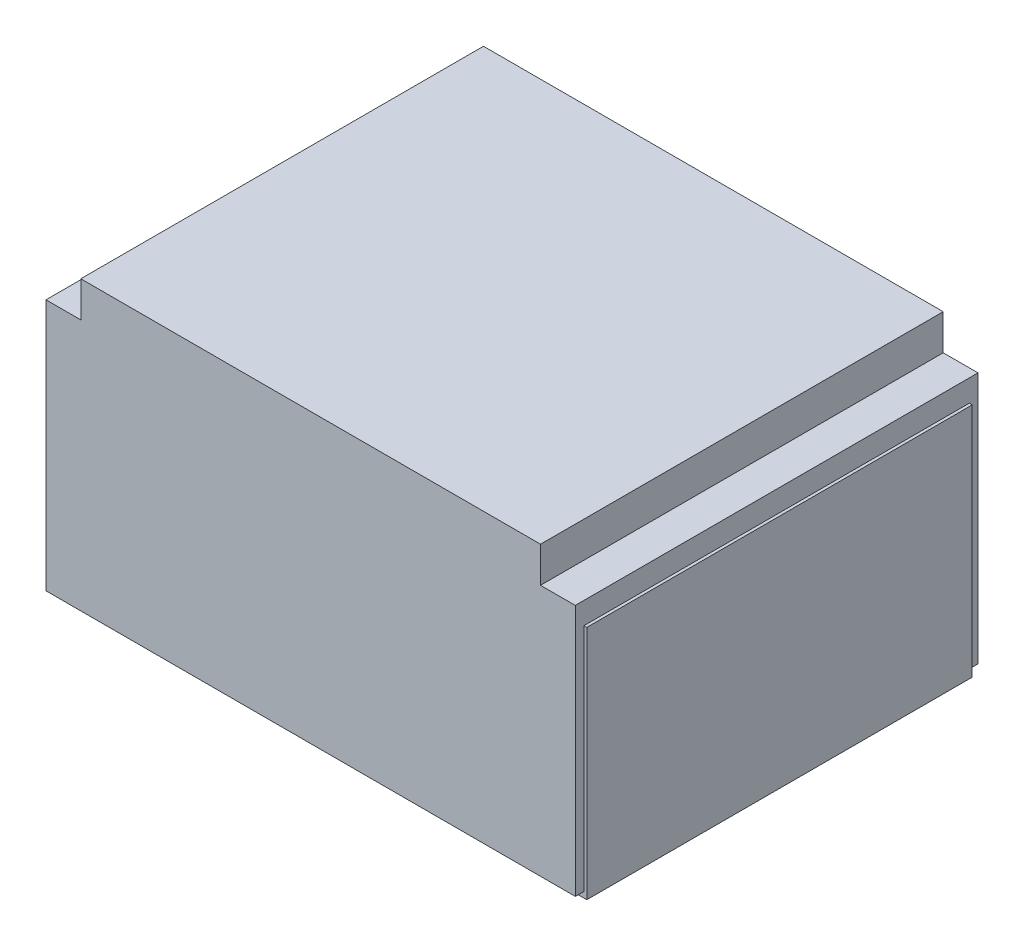
SolidWorks part; units mm, degrees
ref_plane "Płaszczyzna przednia" through (0, 0, 0) normal (0, 0, 1) x (1, 0, 0)
ref_plane "Płaszczyzna górna" through (0, 0, 0) normal (0, 1, 0) x (1, 0, 0)
ref_plane "Płaszczyzna prawa" through (0, 0, 0) normal (1, 0, 0) x (0, 0, -1)
sketch "Szkic1" plane through (0, 0, 0) normal (0, 0, 1) x (1, 0, 0)
  line L1 (2.3, 1.25) -> (-2.3, 1.25)
  line L2 (2.3, 1.25) -> (2.3, -1.25)
  line L3 (2.3, -1.25) -> (-2.3, -1.25)
  line L4 (-2.3, 1.25) -> (-2.3, -1.25)
  line L5 (2.3, 1.25) -> (-2.3, -1.25) construction
  line L6 (2.3, -1.25) -> (-2.3, 1.25) construction
  point P0 (0, 0)
  dimension "D1" = 2.5
  dimension "D2" = 4.6
extrude "Dodanie-wyciągnięcie1" add sketch "Szkic1" along normal blind 3.5
sketch "Szkic2" plane through (0, 0, 3.5) normal (0, 0, 1) x (1, 0, 0)
  line L0 (-2.3, 1.25) -> (-2.3, 0.9406)
  line L1 (-2.3, 1.25) -> (-2.3, -1.25) construction
  line L2 (-2.3, 0.9406) -> (-1.9978, 0.9406)
  line L3 (-1.9978, 0.9406) -> (-1.9978, 1.25)
  line L4 (2.3, 1.25) -> (-2.3, 1.25) construction
  line L5 (-1.9978, 1.25) -> (-2.3, 1.25)
  line L6 (0, 1.25) -> (0, 1.6855) construction
  line L7 (1.9978, 1.25) -> (2.3, 1.25)
  line L8 (1.9978, 0.9406) -> (1.9978, 1.25)
  line L9 (2.3, 0.9406) -> (1.9978, 0.9406)
  line L10 (2.3, 1.25) -> (2.3, 0.9406)
extrude "Wytnij-wyciągnięcie1" cut sketch "Szkic2" against normal through all
sketch "Szkic3" plane through (0, -1.25, 0) normal (0, -1, 0) x (1, 0, 0)
  line L0 (0, 3.5) -> (0, 0) construction
  line L1 (-2.3, 3.5) -> (2.3, 3.5) construction
  line L3 (-2.325, 0.075) -> (2.325, 0.075)
  line L4 (-2.325, 0.075) -> (-2.325, 3.425)
  line L5 (-2.325, 3.425) -> (2.325, 3.425)
  line L6 (2.325, 0.075) -> (2.325, 3.425)
  line L7 (-2.325, 0.075) -> (2.325, 3.425) construction
  line L8 (-2.325, 3.425) -> (2.325, 0.075) construction
  point P5 (0, 1.75)
  dimension "D1" = 3.35
  dimension "D2" = 4.65
extrude "Dodanie-wyciągnięcie2" add sketch "Szkic3" along normal blind 0.05 separate body
sketch "Szkic4" plane through (0, -1.3, 0) normal (0, -1, 0) x (1, 0, 0)
  line L0 (0, 3.425) -> (0, -0.2332) construction
  line L1 (2.325, 3.425) -> (-2.325, 3.425) construction
  line L2 (-1.7482, 0.075) -> (-1.7482, 0.4413)
  line L3 (-2.325, 0.075) -> (2.325, 0.075) construction
  line L4 (-1.7482, 0.4413) -> (-1.6483, 0.4413)
  line L5 (-1.6483, 0.4413) -> (-1.4734, 0.1915)
  line L6 (-1.4734, 0.1915) -> (1.4734, 0.1915)
  line L7 (1.6483, 0.4413) -> (1.4734, 0.1915)
  line L8 (1.7482, 0.4413) -> (1.6483, 0.4413)
  line L9 (1.7482, 0.075) -> (1.7482, 0.4413)
  line L10 (-1.7482, 0.075) -> (1.7482, 0.075)
  circle A0 centre (-1.9231, 3.0894) radius 0.1624
  circle A1 centre (1.9231, 3.0894) radius 0.1624
  circle A2 centre (0, 1.5959) radius 1.05
  point P17 (0, 0.1915)
  dimension "D1" = 2.1
extrude "Wytnij-wyciągnięcie2" cut sketch "Szkic4" against normal up to vertex (0.05 mm away)
sketch "Szkic5" plane through (0, -1.25, 0) normal (0, -1, 0) x (1, 0, 0)
  circle A0 centre (0, 1.5959) radius 1
  dimension "D1" = 2
extrude "Dodanie-wyciągnięcie3" add sketch "Szkic5" along normal blind 0.4 separate body
fillet "Zaokrąglenie1" radius 0.05 1 edges at (1, -1.65, 1.5959)
sketch "Szkic6" plane through (0, -1.25, 0) normal (0, 1, 0) x (1, 0, 0)
  line L0 (-2.325, -0.075) -> (-2.325, -3.425)
  line L1 (-2.325, -3.425) -> (-2.3, -3.425)
  line L2 (-2.3, 0) -> (-2.3, -3.5) construction
  line L3 (2.325, -3.425) -> (-2.325, -3.425) construction
  line L4 (-2.3, -3.425) -> (-2.3, -0.075)
  line L5 (-2.325, -0.075) -> (-1.7482, -0.075) construction
  line L6 (-2.3, -0.075) -> (-2.325, -0.075)
  line L7 (0, -3.5) -> (0, -4.4687) construction
  line L12 (1.9978, -3.5) -> (-1.9978, -3.5) construction
  line L13 (2.3, -0.075) -> (2.325, -0.075)
  line L14 (2.3, -3.425) -> (2.3, -0.075)
  line L15 (2.325, -3.425) -> (2.3, -3.425)
  line L16 (2.325, -0.075) -> (2.325, -3.425)
extrude "Dodanie-wyciągnięcie4" add sketch "Szkic6" along normal blind 2
